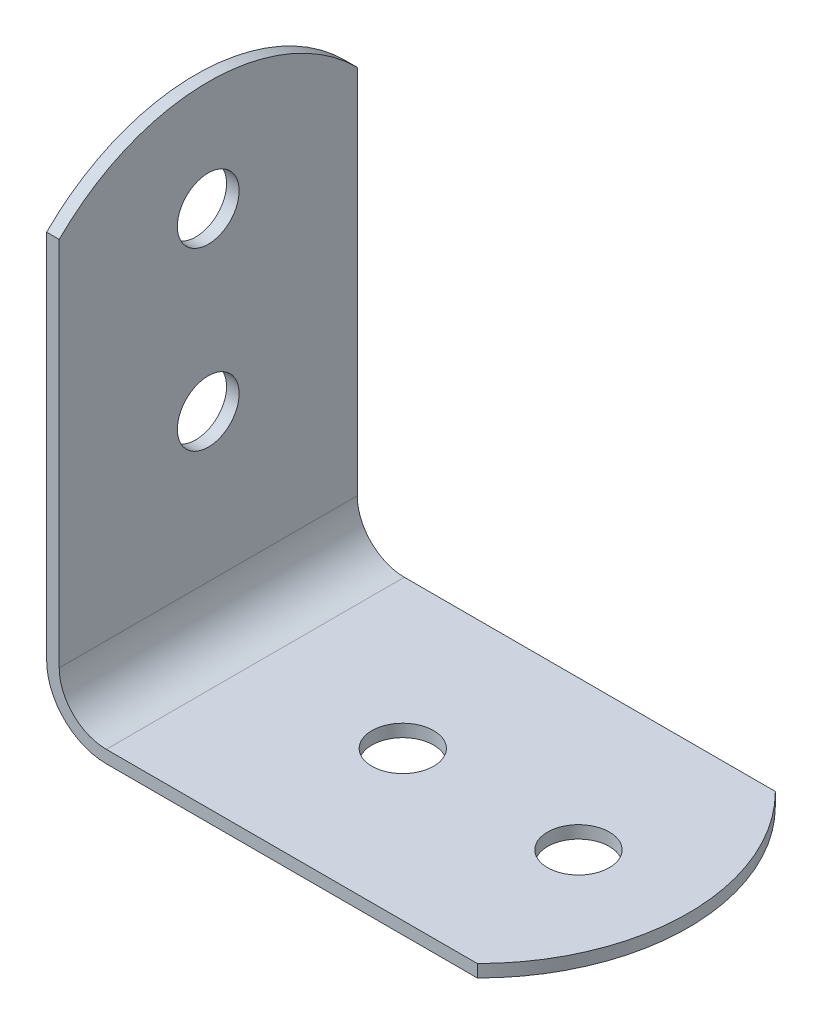
SolidWorks part; units mm, degrees
material "AISI 316 Stainless Steel Sheet (SS)"
ref_plane "Front Plane" through (0, 0, 0) normal (0, 0, 1) x (1, 0, 0)
ref_plane "Top Plane" through (0, 0, 0) normal (0, 1, 0) x (1, 0, 0)
ref_plane "Right Plane" through (0, 0, 0) normal (1, 0, 0) x (0, 0, -1)
sketch "Sketch1" plane through (0, 0, 0) normal (0, 0, 1) x (1, 0, 0)
  line L0 (0, 39.878) -> (0, 0)
  line L1 (0, 0) -> (39.878, 0)
  line L2 (39.878, 0) -> (39.878, 1.016)
  line L3 (39.878, 1.016) -> (1.016, 1.016)
  line L4 (1.016, 1.016) -> (1.016, 39.878)
  line L5 (1.016, 39.878) -> (0, 39.878)
  dimension "D1" = 39.878
  dimension "D2" = 1.016
extrude "Boss-Extrude1" add sketch "Sketch1" along normal blind 24.13
fillet "Fillet1" radius 3.81 1 edges at (1.016, 1.016, 12.065)
fillet "Fillet2" radius 4.826 1 edges at (0, 0, 12.065)
hole_wizard "Ø5.0mm Dowel Hole1" positions "Sketch2" profile "Sketch3" hole size "Ø5.0" standard "ANSI Metric" end condition through all
sketch "Sketch2" plane through (0, 0, 0) normal (-1, 0, 0) x (0, 0, 1)
  line L1 (24.13, 0) -> (0, 0) construction
  line L2 (0, 39.878) -> (0, 4.826) construction
  point P0 (12.065, 30.988)
  point P2 (12.065, 16.764)
  point P11 (9.9669, 32.2516)
  point P12 (0, 0)
  point P21 (12.065, 16.764)
  point P22 (0, 0)
  dimension "D1" = 16.764
  dimension "D2" = 14.224
  dimension "D3" = 12.065
sketch "Sketch3" plane through (0, 30.988, 12.065) normal (0, 1, 0) x (0, 0, 1)
  line L0 (0, 0) -> (0, 39.878)
  line L1 (0, 39.878) -> (2.5, 39.878)
  line L2 (2.5, 39.878) -> (2.5, 0)
  line L5 (2.5, 0) -> (0, 0)
  line L11 (0, -6.35) -> (0, 107.95) construction
  dimension "Thru Hole Dia." = 5
  dimension "Thru Hole Depth" = 39.878
hole_wizard "Ø5.0mm Dowel Hole2" positions "Sketch4" profile "Sketch5" hole size "Ø5.0" standard "ANSI Metric" end condition through all
sketch "Sketch4" plane through (0, 0, 0) normal (0, -1, 0) x (-1, 0, 0)
  line L0 (-4.826, -24.13) -> (-39.878, -24.13) construction
  line L1 (0, 0) -> (0, -24.13) construction
  point P0 (-30.988, -12.065)
  point P2 (-16.764, -12.065)
  dimension "D1" = 12.065
  dimension "D2" = 16.764
  dimension "D3" = 14.224
sketch "Sketch5" plane through (30.988, 0, 12.065) normal (1, 0, 0) x (0, 0, -1)
  line L0 (0, 0) -> (0, 39.878)
  line L1 (0, 39.878) -> (2.5, 39.878)
  line L2 (2.5, 39.878) -> (2.5, 0)
  line L5 (2.5, 0) -> (0, 0)
  line L11 (0, -6.35) -> (0, 107.95) construction
  dimension "Thru Hole Dia." = 5
  dimension "Thru Hole Depth" = 39.878
sketch "Sketch6" plane through (0, 0, 0) normal (0, -1, 0) x (1, 0, 0)
  line L0 (4.826, 24.13) -> (39.878, 24.13) construction
  line L1 (4.826, 0) -> (39.878, 0) construction
  line L2 (39.878, 24.13) -> (39.878, 0) construction
  line L3 (0, 0) -> (0, 24.13) construction
  line L4 (34.862, 24.13) -> (44.45, 24.13)
  line L5 (44.45, 24.13) -> (44.45, 0)
  line L6 (44.45, 0) -> (34.862, 0)
  arc A0 (34.862, 24.13) -> (34.862, 0) centre (22.86, 12.065) cw
  dimension "D1" = 12.065
  dimension "D2" = 22.86
  dimension "D3" = 44.45
extrude "Cut-Extrude1" cut sketch "Sketch6" against normal through all
sketch "Sketch7" plane through (0, 0, 0) normal (-1, 0, 0) x (0, 0, 1)
  line L0 (0, 39.878) -> (0, 4.826) construction
  line L1 (24.13, 39.878) -> (24.13, 4.826) construction
  line L2 (24.13, 39.878) -> (0, 39.878) construction
  line L3 (24.13, 0) -> (0, 0) construction
  line L4 (0, 34.862) -> (0, 44.45)
  line L5 (0, 44.45) -> (24.13, 44.45)
  line L6 (24.13, 44.45) -> (24.13, 34.862)
  arc A0 (0, 34.862) -> (24.13, 34.862) centre (12.065, 22.86) cw
  dimension "D1" = 12.065
  dimension "D2" = 22.86
  dimension "D3" = 44.45
extrude "Cut-Extrude2" cut sketch "Sketch7" against normal through all
